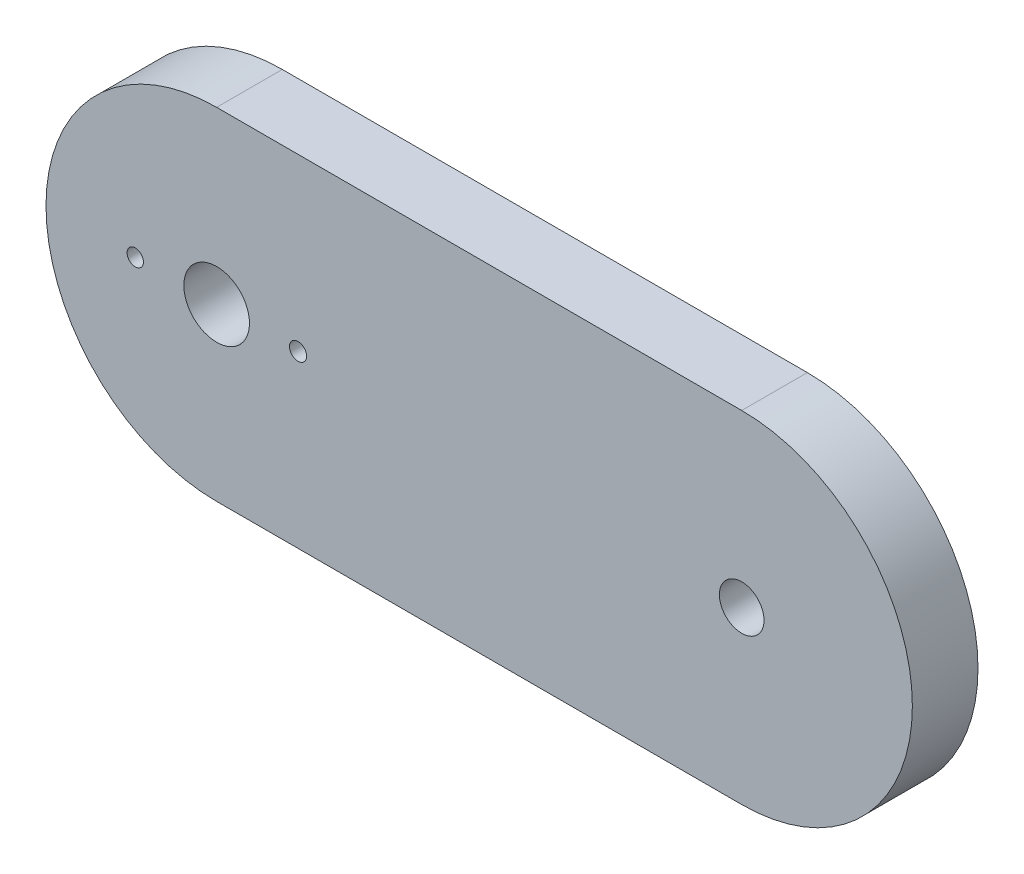
SolidWorks part; units mm, degrees
ref_plane "Front Plane" through (0, 0, 0) normal (0, 0, 1) x (1, 0, 0)
ref_plane "Top Plane" through (0, 0, 0) normal (0, 1, 0) x (1, 0, 0)
ref_plane "Right Plane" through (0, 0, 0) normal (1, 0, 0) x (0, 0, -1)
sketch "Sketch1" plane through (0, 0, 0) normal (0, 0, 1) x (1, 0, 0)
  line L1 (-25.4, 16.51) -> (25.4, 16.51)
  line L2 (-25.4, 16.51) -> (-25.4, -16.51)
  line L3 (-25.4, -16.51) -> (25.4, -16.51)
  line L4 (25.4, 16.51) -> (25.4, -16.51)
  line L5 (-25.4, 16.51) -> (25.4, -16.51) construction
  line L6 (-25.4, -16.51) -> (25.4, 16.51) construction
  line L11 (-12.7, 8.89) -> (12.7, -8.89) construction
  line L12 (-12.7, -8.89) -> (12.7, 8.89) construction
  arc A0 (25.4, -16.51) -> (25.4, 16.51) centre (25.4, 0) ccw
  arc A1 (-25.4, -16.51) -> (-25.4, 16.51) centre (-25.4, 0) cw
  circle A2 centre (25.4, 0) radius 2.159
  circle A3 centre (-25.4, 0) radius 3.175
  point P0 (0, 0)
  point P10 (0, 0)
  dimension "D3" = 6.35
  dimension "D4" = 4.318
  dimension "D1" = 33.02
  dimension "D2" = 50.8
extrude "Boss-Extrude1" add sketch "Sketch1" along normal blind 6.35
sketch "Sketch2" plane through (0, 0, 6.35) normal (0, 0, 1) x (1, 0, 0)
  circle A0 centre (25.4, 0) radius 7.7596
  circle A1 centre (25.4, 0) radius 3.81
  dimension "D1" = 7.62
extrude "Boss-Extrude2" add sketch "Sketch2" against normal blind 1.27
sketch "Sketch3" plane through (0, 0, 0) normal (0, 0, -1) x (-1, 0, 0)
  circle A0 centre (17.526, 0) radius 0.8295
  circle A1 centre (33.274, 0) radius 0.7928
  circle A2 centre (25.4, 0) radius 3.175 construction
  dimension "D2" = 7.874
  dimension "D1" = 7.874
extrude "Cut-Extrude1" cut sketch "Sketch3" against normal blind 17.272
